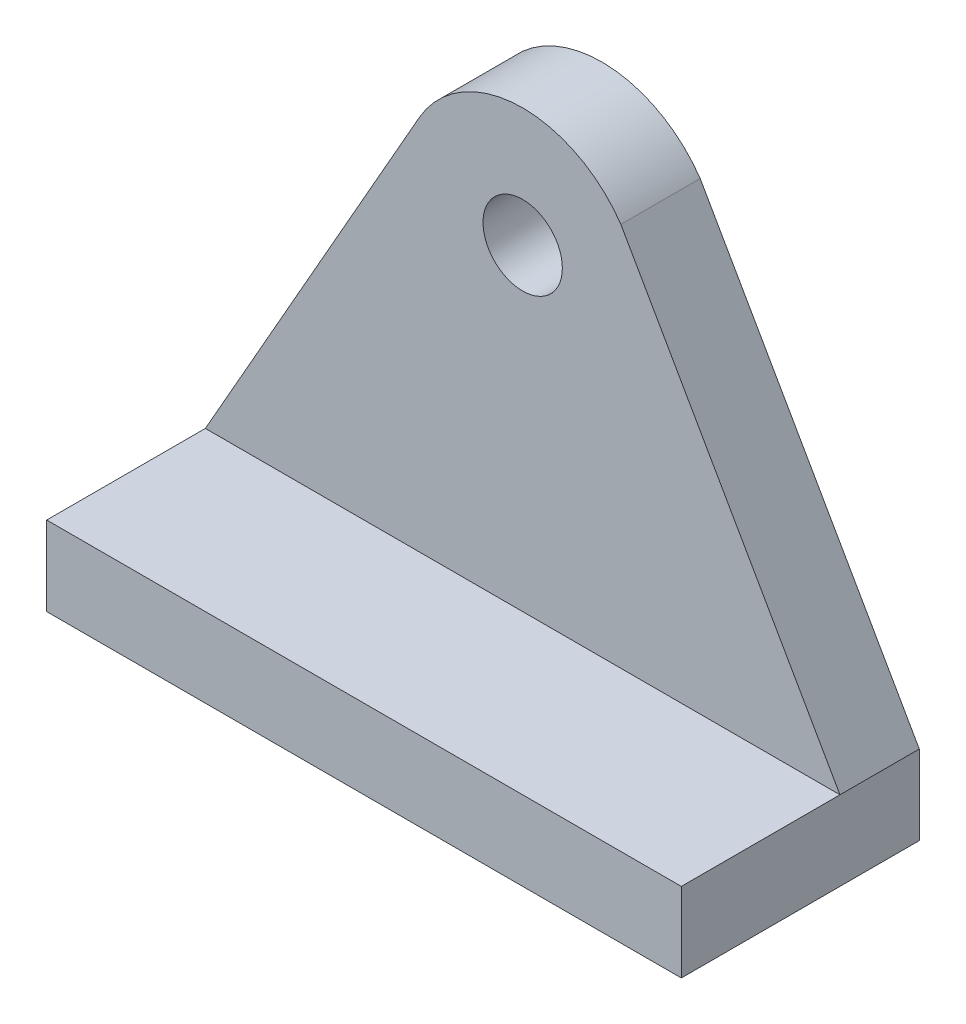
SolidWorks part; units mm, degrees
ref_plane "前视基准面" through (0, 0, 0) normal (0, 0, 1) x (1, 0, 0)
ref_plane "上视基准面" through (0, 0, 0) normal (0, 1, 0) x (1, 0, 0)
ref_plane "右视基准面" through (0, 0, 0) normal (1, 0, 0) x (0, 0, -1)
sketch "草图1" plane through (0, 0, 0) normal (0, 0, 1) x (1, 0, 0)
  line L0 (0, 0) -> (0, -1)
  line L1 (0, -8) -> (-8, -8)
  line L2 (0, -8) -> (8, -8)
  line L3 (8, -8) -> (2.4756, 1.6945)
  line L4 (-8, -8) -> (-2.6079, 1.4829)
  arc A0 (2.7197, 1.2661) -> (-2.6079, 1.4829) centre (0, 0) ccw
  circle A1 centre (0, 0) radius 1
  dimension "D1" = 2
  dimension "D2" = 6
  dimension "D3" = 8
  dimension "D4" = 8
  dimension "D5" = 8
extrude "凸台-拉伸1" add sketch "草图1" along normal blind 2 contours L3 A0 L4 L1 L2 A1
sketch "草图2" plane through (0, 0, 0) normal (0, 0, -1) x (-1, 0, 0)
  line L1 (-8, -8) -> (8, -8)
  line L2 (-8, -8) -> (-8, -10)
  line L3 (-8, -10) -> (8, -10)
  line L4 (8, -8) -> (8, -10)
  dimension "D1" = 2
extrude "凸台-拉伸2" add sketch "草图2" against normal blind 6
